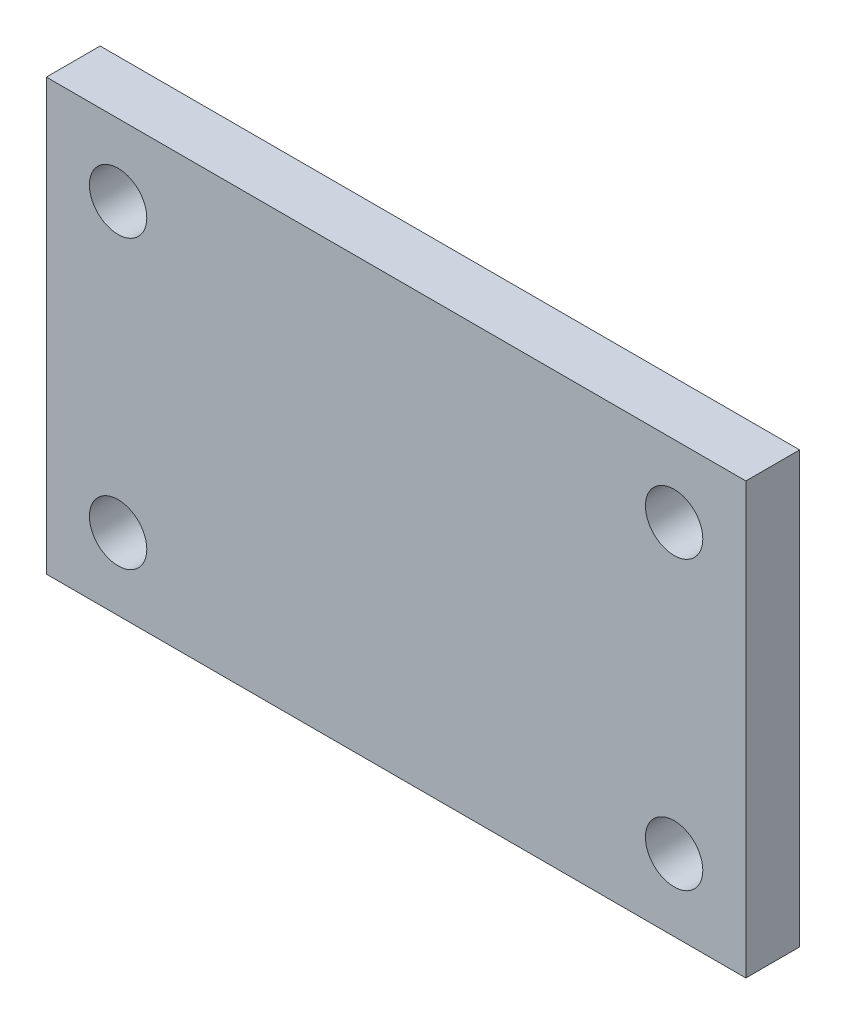
SolidWorks part; units mm, degrees
ref_plane "正面" through (0, 0, 0) normal (0, 0, 1) x (1, 0, 0)
ref_plane "平面" through (0, 0, 0) normal (0, 1, 0) x (1, 0, 0)
ref_plane "右側面" through (0, 0, 0) normal (1, 0, 0) x (0, 0, -1)
sketch "ｽｹｯﾁ1" plane through (0, 0, 0) normal (0, 0, 1) x (1, 0, 0)
  line L1 (-19.5, 10) -> (19.5, 10)
  line L2 (-19.5, 10) -> (-19.5, -10)
  line L3 (-19.5, -10) -> (19.5, -10)
  line L4 (19.5, 10) -> (19.5, -10)
  line L5 (-19.5, 10) -> (19.5, -10) construction
  line L6 (-19.5, -10) -> (19.5, 10) construction
  line L7 (-19.5, -10) -> (-15.5, -10)
  line L8 (-19.5, -10) -> (-19.5, -10)
  line L9 (-19.5, -10) -> (-15.5, -10)
  line L11 (-19.5, 10) -> (-15.5, 10)
  line L12 (-19.5, 10) -> (-19.5, 6)
  line L13 (-19.5, 6) -> (-15.5, 6)
  line L14 (-15.5, 10) -> (-15.5, 6)
  line L15 (19.5, 10) -> (15.5, 10)
  line L16 (19.5, 10) -> (19.5, 6)
  line L17 (19.5, 6) -> (15.5, 6)
  line L18 (15.5, 10) -> (15.5, 6)
  line L19 (19.5, -10) -> (15.5, -10)
  line L20 (19.5, -10) -> (19.5, -10)
  line L21 (19.5, -10) -> (15.5, -10)
  circle A0 centre (-15.5, 6) radius 1.6
  circle A2 centre (15.5, 6) radius 1.6
  point P0 (0, 0)
  dimension "D11" = 3.2
  dimension "D13" = 3.2
  dimension "D1" = 20
  dimension "D2" = 39
  dimension "D5" = 4
  dimension "D6" = 4
  dimension "D9" = 4
  dimension "D10" = 4
extrude "ﾎﾞｽ - 押し出し1" add sketch "ｽｹｯﾁ1" along normal blind 3
sketch "ｽｹｯﾁ2" plane through (0, -10, 0) normal (0, -1, 0) x (1, 0, 0)
  line L0 (-19.5, 3) -> (19.5, 3) construction
  line L1 (-19.5, 0) -> (19.5, 0)
  line L2 (-19.5, 0) -> (-19.5, 3)
  line L3 (-19.5, 3) -> (19.5, 3)
  line L4 (19.5, 0) -> (19.5, 3)
  line L5 (19.5, 3) -> (19.5, 0) construction
extrude "ﾎﾞｽ - 押し出し2" add sketch "ｽｹｯﾁ2" along normal blind 4
sketch "ｽｹｯﾁ3" plane through (0, 0, 3) normal (0, 0, 1) x (1, 0, 0)
  line L0 (-15.5, 6) -> (-15.5, -10)
  line L1 (15.5, 6) -> (15.5, -10)
  circle A0 centre (-15.5, 6) radius 1.6
  circle A1 centre (-15.5, -10) radius 1.6
  circle A2 centre (15.5, -10) radius 1.6
  dimension "D3" = 3.2
  dimension "D4" = 3.2
  dimension "D5" = 3.2
  dimension "D1" = 16
  dimension "D2" = 16
extrude "ｶｯﾄ - 押し出し1" cut sketch "ｽｹｯﾁ3" against normal blind 4
